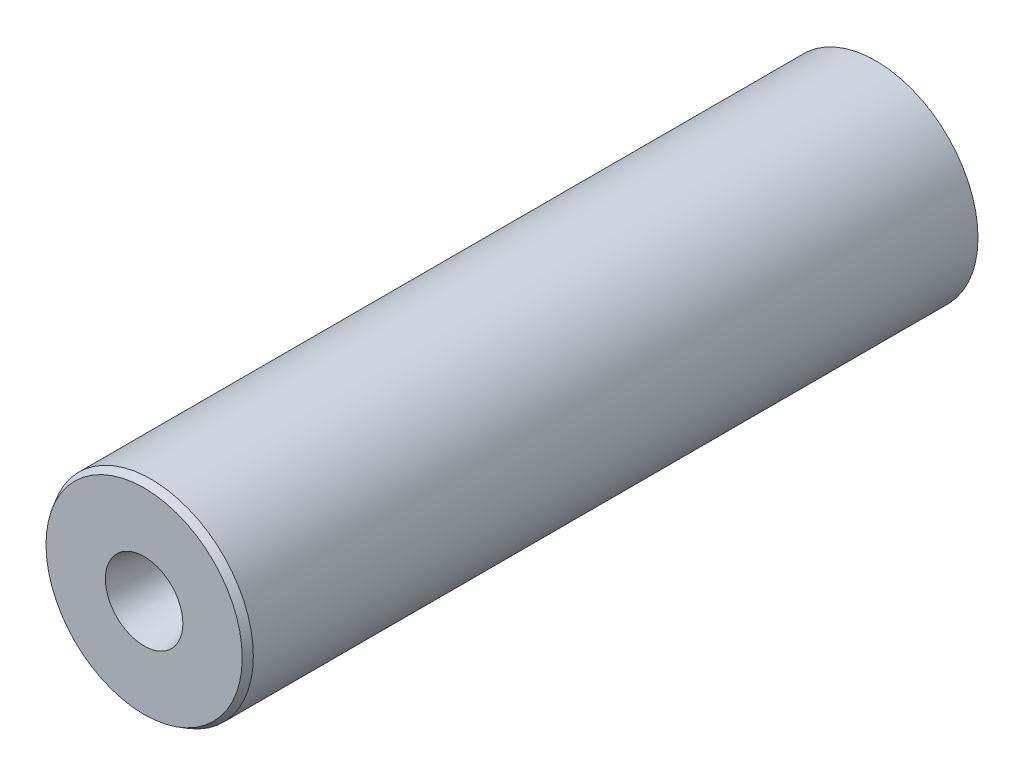
SolidWorks part; units mm, degrees
material "PLA"
ref_plane "Plan de face" through (0, 0, 0) normal (0, 0, 1) x (1, 0, 0)
ref_plane "Plan de dessus" through (0, 0, 0) normal (0, 1, 0) x (1, 0, 0)
ref_plane "Plan de droite" through (0, 0, 0) normal (1, 0, 0) x (0, 0, -1)
sketch "Esquisse1" plane through (0, 0, 0) normal (1, 0, 0) x (0, 0, -1)
  line L0 (-51.9182, 0) -> (51.9182, 0) construction
  line L1 (36.9182, 11) -> (36.9182, 9)
  line L2 (-51.9182, 14.5) -> (51.9182, 14.5)
  line L4 (-23.0818, 11) -> (36.9182, 11)
  line L6 (36.9182, 9) -> (51.9182, 9)
  line L7 (51.9182, 14.5) -> (51.9182, 9)
  line L8 (-23.0818, 11) -> (-37.8043, 2.5)
  line L9 (-37.8043, 2.5) -> (-51.9182, 5.5)
  line L10 (-51.9182, 14.5) -> (-51.9182, 5.5)
  line L11 (-47.6261, 7.6547) -> (-41.6462, 6.3836) construction
  line L12 (-47.4182, 11.5) -> (-33.9479, 11.5) construction
  line L13 (-48.4182, 10.5) -> (-48.4182, 8.6329) construction
  line L16 (-38.1066, 6.9443) -> (-33.4479, 9.634) construction
  arc A0 (-33.9479, 11.5) -> (-33.4479, 9.634) centre (-33.9479, 10.5) cw construction
  arc A1 (-48.4182, 8.6329) -> (-47.6261, 7.6547) centre (-47.4182, 8.6329) ccw construction
  arc A2 (-47.4182, 11.5) -> (-48.4182, 10.5) centre (-47.4182, 10.5) ccw construction
  arc A3 (-41.6462, 6.3836) -> (-38.1066, 6.9443) centre (-40.6066, 11.2744) ccw construction
  dimension "D14" = 1
  dimension "D15" = 5
  dimension "D1" = 60
  dimension "D2" = 11
  dimension "D3" = 14.5
  dimension "D4" = 15
  dimension "D5" = 9
  dimension "D6" = 2.5
  dimension "D7" = 30
  dimension "D8" = 12
  dimension "D9" = 5.5
  dimension "D10" = 3.5
  dimension "D11" = 3
  dimension "D12" = 3
  dimension "D13" = 4
revolve "Révolution1" add sketch "Esquisse1" angle 360 about L0
ref_plane "Plan de face-Bouchon" through (0, 0, -50.3375) normal (0, 0, -1) x (1, 0, 0)
ref_plane "Plan de dessus-Bouchon" through (0, 0, -50.3375) normal (0, -1, 0) x (1, 0, 0)
ref_plane "Plan de droite-Bouchon" through (0, 0, -50.3375) normal (1, 0, 0) x (0, 0, 1)
inserted part "Bouchon"
move or copy body "Corps-Déplacer/Copier2"
other "Embouti1" [suppressed] parameters "D1"=10, "D2"=0.2
sketch "Esquisse2" plane through (0, 0, -51.9182) normal (0, 0, -1) x (-1, 0, 0)
  circle A0 centre (0, 0) radius 11
  circle A1 centre (0, 0) radius 11 construction
extrude "Enlèv. mat.-Extru.1" cut sketch "Esquisse2" against normal up to surface (15 mm away) up to face at (9, 0, -36.9182)
sketch "Esquisse3" plane through (0, 0, 0) normal (1, 0, 0) x (0, 0, -1)
  line L0 (48.9182, 11) -> (48.9182, 12)
  line L1 (51.9182, 11) -> (-23.0818, 11) construction
  line L2 (48.9182, 12) -> (46.9182, 12)
  line L3 (46.9182, 12) -> (46.9182, 11)
  line L4 (46.9182, 11) -> (43.9182, 11)
  line L5 (43.9182, 11) -> (43.9182, 12)
  line L6 (43.9182, 12) -> (41.9182, 12)
  line L7 (41.9182, 12) -> (41.9182, 11)
  line L8 (41.9182, 11) -> (38.9182, 11)
  line L9 (38.9182, 11) -> (38.9182, 12)
  line L10 (38.9182, 12) -> (36.9182, 12)
  line L11 (36.9182, 12) -> (36.9182, 11)
  line L12 (48.9182, 11) -> (51.9182, 11)
  line L13 (51.9182, -14.5) -> (51.9182, 14.5) construction
  line L14 (0, 0) -> (51.9182, 0) construction
  line L15 (36.9182, 11) -> (36.9182, 0)
  line L16 (51.9182, 11) -> (51.9182, 0)
  line L17 (51.9182, 0) -> (36.9182, 0)
  line L18 (-23.0818, 11) -> (-23.0818, -11) construction
  dimension "D1" = 60
  dimension "D2" = 2
  dimension "D3" = 1
revolve "Enlèvement de matière-Révolution1" cut sketch "Esquisse3" angle 360 about L14
fillet "Congé1" radius 5 2 edges at (2.5, 0, 37.8043) (11, 0, 23.0818)
chamfer "Chanfrein1" distance 1 angle 30 1 edges at (14.5, 0, 51.9182)
